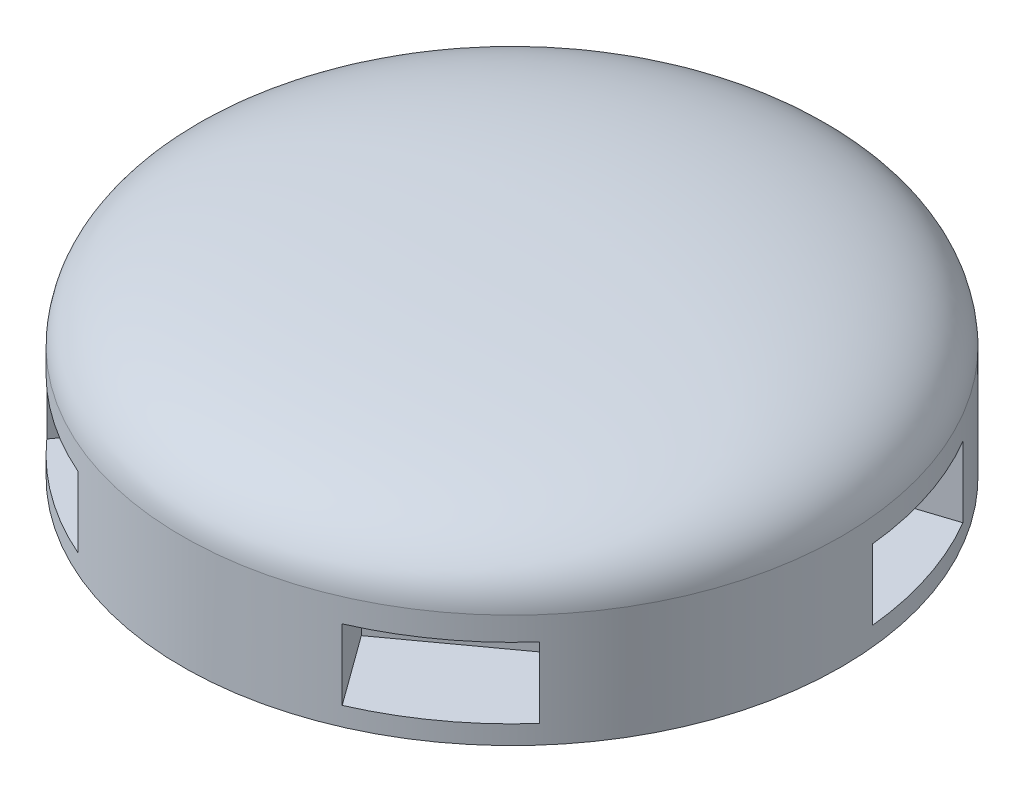
SolidWorks part; units mm, degrees
ref_plane "Plan de face" through (0, 0, 0) normal (0, 0, 1) x (1, 0, 0)
ref_plane "Plan de dessus" through (0, 0, 0) normal (0, 1, 0) x (1, 0, 0)
ref_plane "Plan de droite" through (0, 0, 0) normal (1, 0, 0) x (0, 0, -1)
sketch "Esquisse2" plane through (0, 0, 0) normal (0, 0, 1) x (1, 0, 0)
  line L0 (0, 20) -> (0, 0)
  line L1 (0, 0) -> (35, 0)
  line L2 (35, 0) -> (35, 10)
  line L3 (25.8795, 20) -> (-25.8795, 20) construction
  spline S0 degree 3 poles (0, 20) (32.3494, 20) (34.8018, 13.4311) (35, 10) knots 0 0 0 0 1 1 1 1
  point P8 (0, 0)
  dimension "D3" = 35
  dimension "D1" = 10
  dimension "D2" = 20
revolve "Révolution1" add sketch "Esquisse2" angle 360 about L0
ref_plane "Plan1" through (35, 0, 0) normal (1, 0, 0) x (0, 0, -1)
sketch "Esquisse3" plane through (0, 0, 0) normal (0, -1, 0) x (1, 0, 0)
  line L0 (0, -55) -> (0, 55) construction
  line L1 (-7.5, -45) -> (7.5, -45)
  line L2 (-7.5, -45) -> (-7.5, -25)
  line L3 (-7.5, -25) -> (7.5, -25)
  line L4 (7.5, -45) -> (7.5, -25)
  line L5 (-7.5, -45) -> (7.5, -25) construction
  line L6 (-7.5, -25) -> (7.5, -45) construction
  line L7 (-42.7211, -16.0048) -> (-17.9006, -18.9952) construction
  line L8 (-25.4006, -6.0048) -> (-35.2211, -28.9952) construction
  line L13 (-35.2211, 28.9952) -> (-25.4006, 6.0048) construction
  line L14 (-17.9006, 18.9952) -> (-42.7211, 16.0048) construction
  line L19 (7.5, 45) -> (-7.5, 25) construction
  line L20 (7.5, 25) -> (-7.5, 45) construction
  line L25 (42.7211, 16.0048) -> (17.9006, 18.9952) construction
  line L26 (25.4006, 6.0048) -> (35.2211, 28.9952) construction
  line L31 (35.2211, -28.9952) -> (25.4006, -6.0048) construction
  line L32 (17.9006, -18.9952) -> (42.7211, -16.0048) construction
  line L37 (35.2211, -28.9952) -> (17.9006, -18.9952) [skipped]
  line L38 (17.9006, -18.9952) -> (25.4006, -6.0048) [skipped]
  line L39 (42.7211, -16.0048) -> (25.4006, -6.0048) [skipped]
  line L40 (35.2211, -28.9952) -> (42.7211, -16.0048) [skipped]
  line L41 (42.7211, 16.0048) -> (25.4006, 6.0048) [skipped]
  line L42 (25.4006, 6.0048) -> (17.9006, 18.9952) [skipped]
  line L43 (35.2211, 28.9952) -> (17.9006, 18.9952) [skipped]
  line L44 (42.7211, 16.0048) -> (35.2211, 28.9952) [skipped]
  line L45 (7.5, 45) -> (7.5, 25) [skipped]
  line L46 (7.5, 25) -> (-7.5, 25) [skipped]
  line L47 (-7.5, 45) -> (-7.5, 25) [skipped]
  line L48 (7.5, 45) -> (-7.5, 45) [skipped]
  line L49 (-35.2211, 28.9952) -> (-17.9006, 18.9952) [skipped]
  line L50 (-17.9006, 18.9952) -> (-25.4006, 6.0048) [skipped]
  line L51 (-42.7211, 16.0048) -> (-25.4006, 6.0048) [skipped]
  line L52 (-35.2211, 28.9952) -> (-42.7211, 16.0048) [skipped]
  line L53 (-42.7211, -16.0048) -> (-25.4006, -6.0048) [skipped]
  line L54 (-25.4006, -6.0048) -> (-17.9006, -18.9952) [skipped]
  line L55 (-35.2211, -28.9952) -> (-17.9006, -18.9952) [skipped]
  line L56 (-42.7211, -16.0048) -> (-35.2211, -28.9952) [skipped]
  line L57 (-45.1152, -6.7728) -> (-26.094, -0.5925)
  line L58 (-45.1152, -6.7728) -> (-40.4799, -21.0387)
  line L59 (-40.4799, -21.0387) -> (-21.4588, -14.8583)
  line L60 (-26.094, -0.5925) -> (-21.4588, -14.8583)
  line L61 (-20.3827, 40.8142) -> (-8.627, 24.6338)
  line L62 (-20.3827, 40.8142) -> (-32.518, 31.9974)
  line L63 (-32.518, 31.9974) -> (-20.7623, 15.817)
  line L64 (-8.627, 24.6338) -> (-20.7623, 15.817)
  line L65 (32.518, 31.9974) -> (20.7623, 15.817)
  line L66 (32.518, 31.9974) -> (20.3827, 40.8142)
  line L67 (20.3827, 40.8142) -> (8.627, 24.6338)
  line L68 (20.7623, 15.817) -> (8.627, 24.6338)
  line L69 (40.4799, -21.0387) -> (21.4588, -14.8583)
  line L70 (40.4799, -21.0387) -> (45.1152, -6.7728)
  line L71 (45.1152, -6.7728) -> (26.094, -0.5925)
  line L72 (21.4588, -14.8583) -> (26.094, -0.5925)
  circle A0 centre (0, 0) radius 35 construction
  point P0 (0, -35)
  point P11 (-30.3109, -17.5)
  point P16 (-30.3109, 17.5)
  point P21 (0, 35)
  point P26 (30.3109, 17.5)
  point P31 (30.3109, -17.5)
  point P36 (0, 0)
  point P93 (0, 0)
  dimension "D1" = 6
  dimension "D2" = 15
  dimension "D3" = 20
  dimension "D4" = 5
extrude "Enlèv. mat.-Extru.1" cut sketch "Esquisse3" against normal blind 7.5
sketch "Esquisse4" plane through (0, 0, 0) normal (0, -1, 0) x (1, 0, 0)
  circle A0 centre (0, 0) radius 35
extrude "Boss.-Extru.1" add sketch "Esquisse4" along normal blind 2
